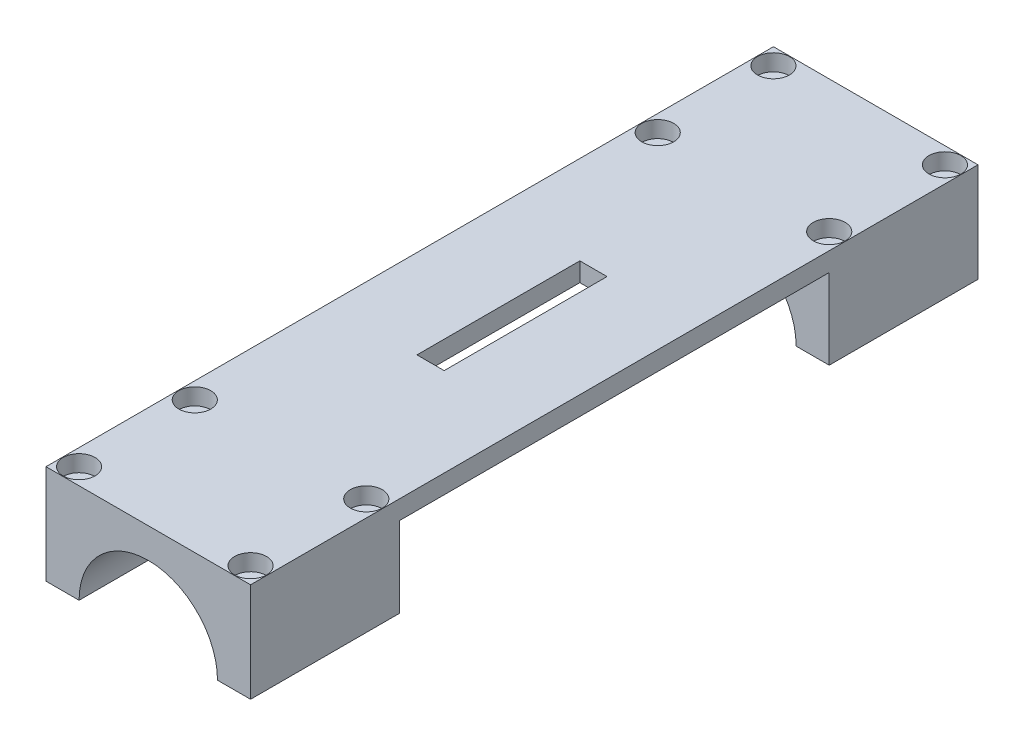
SolidWorks part; units mm, degrees
ref_plane "Plan de face" through (0, 0, 0) normal (0, 0, 1) x (1, 0, 0)
ref_plane "Plan de dessus" through (0, 0, 0) normal (0, 1, 0) x (1, 0, 0)
ref_plane "Plan de droite" through (0, 0, 0) normal (1, 0, 0) x (0, 0, -1)
sketch "Esquisse1" plane through (0, 0, 0) normal (0, 0, 1) x (1, 0, 0)
  line L0 (0, 0) -> (-84.6745, 0) construction
  line L1 (0, 0) -> (94.0931, 0) construction
  line L2 (-12.5601, 0) -> (-18.5601, 0)
  line L3 (0, 0) -> (0, 12.5601) construction
  line L4 (-18.5601, 0) -> (-18.5601, 18)
  line L5 (-18.5601, 18) -> (18.5601, 18)
  line L6 (18.5601, 0) -> (18.5601, 18)
  line L7 (12.5601, 0) -> (18.5601, 0)
  line L8 (0, 12.5601) -> (0, 18) construction
  arc A0 (-12.5601, 0) -> (12.5601, 0) centre (0, 0) cw
  point P11 (0, 18)
  dimension "D1" = 6
  dimension "D2" = 18
extrude "Boss.-Extru.1" add sketch "Esquisse1" along normal blind 132
sketch "Esquisse2" plane through (-18.5601, 0, 0) normal (-1, 0, 0) x (0, 0, 1)
  line L0 (105, 18) -> (105, 0) construction
  line L1 (132, 18) -> (0, 18) construction
  line L2 (132, 0) -> (0, 0) construction
  line L3 (66, 18) -> (66, 0) construction
  line L4 (132, 18) -> (132, 0) construction
  line L5 (66, 14.57) -> (132, 14.57) construction
  line L6 (105, 0) -> (105, 14.57)
  line L7 (105, 14.57) -> (27, 14.57)
  line L8 (105, 0) -> (27, 0)
  line L9 (27, 0) -> (27, 14.57)
  dimension "D1" = 27
  dimension "D2" = 3.43
extrude "Enlèv. mat.-Extru.1" cut sketch "Esquisse2" against normal blind 132
sketch "Esquisse3" plane through (0, 14.57, 0) normal (0, -1, 0) x (1, 0, 0)
  line L0 (-18.5601, 66) -> (18.5601, 66) construction
  line L1 (-18.5601, 105) -> (-18.5601, 27) construction
  line L2 (18.5601, 105) -> (18.5601, 27) construction
  line L3 (0, 66) -> (0, 73.4675) construction
  line L5 (2.4701, 51.2219) -> (-2.4701, 51.2219)
  line L6 (2.4701, 51.2219) -> (2.4701, 80.7781)
  line L7 (2.4701, 80.7781) -> (-2.4701, 80.7781)
  line L8 (-2.4701, 51.2219) -> (-2.4701, 80.7781)
  line L9 (2.4701, 51.2219) -> (-2.4701, 80.7781) construction
  line L10 (2.4701, 80.7781) -> (-2.4701, 51.2219) construction
extrude "Enlèv. mat.-Extru.2" cut sketch "Esquisse3" against normal blind 4
sketch "Esquisse4" plane through (0, 18, 0) normal (0, 1, 0) x (1, 0, 0)
  line L0 (18.5601, -13.5) -> (-19.7679, -13.5) construction
  line L1 (0, 0) -> (0, -28.5028) construction
  line L2 (15.5601, 0) -> (15.5601, -28.5028) construction
  line L3 (18.5601, -3) -> (-18.4211, -3) construction
  line L4 (18.5601, 0) -> (-18.5601, 0) construction
  line L5 (18.5601, -132) -> (18.5601, 0) construction
  line L6 (18.5601, -66) -> (-18.5601, -66) construction
  line L7 (-18.5601, -132) -> (-18.5601, 0) construction
  circle A0 centre (15.5601, -3) radius 1.3
  circle A1 centre (15.5601, -24) radius 1.3
  circle A2 centre (-15.5601, -3) radius 1.3
  circle A3 centre (-15.5601, -24) radius 1.3
  circle A4 centre (-15.5601, -108) radius 1.3
  circle A5 centre (-15.5601, -129) radius 1.3
  circle A6 centre (15.5601, -108) radius 1.3
  circle A7 centre (15.5601, -129) radius 1.3
  dimension "D1" = 3
  dimension "D2" = 3
  dimension "D3" = 10.5
extrude "Enlèv. mat.-Extru.3" cut sketch "Esquisse4" against normal blind 18
sketch "Esquisse6" plane through (0, 18, 0) normal (0, 1, 0) x (1, 0, 0)
  line L0 (18.4241, -13.5) -> (-19.9039, -13.5) construction
  line L1 (0, 0) -> (0, -29.5385) construction
  line L2 (15.5601, 0) -> (15.5601, -29.5385) construction
  line L3 (18.5601, -3) -> (-18.4532, -3) construction
  line L4 (18.5601, -66) -> (-18.696, -66) construction
  line L5 (18.5601, -132) -> (18.5601, 0) construction
  line L6 (18.5601, 0) -> (-18.5601, 0) construction
  circle A0 centre (15.5601, -3) radius 2.9
  circle A1 centre (15.5601, -24) radius 2.9
  circle A2 centre (-15.5601, -3) radius 2.9
  circle A3 centre (-15.5601, -24) radius 2.9
  circle A4 centre (-15.5601, -108) radius 2.9
  circle A5 centre (-15.5601, -129) radius 2.9
  circle A6 centre (15.5601, -108) radius 2.9
  circle A7 centre (15.5601, -129) radius 2.9
  dimension "D1" = 3
  dimension "D2" = 3
  dimension "D3" = 10.5
extrude "Enlèv. mat.-Extru.5" cut sketch "Esquisse6" against normal blind 3
